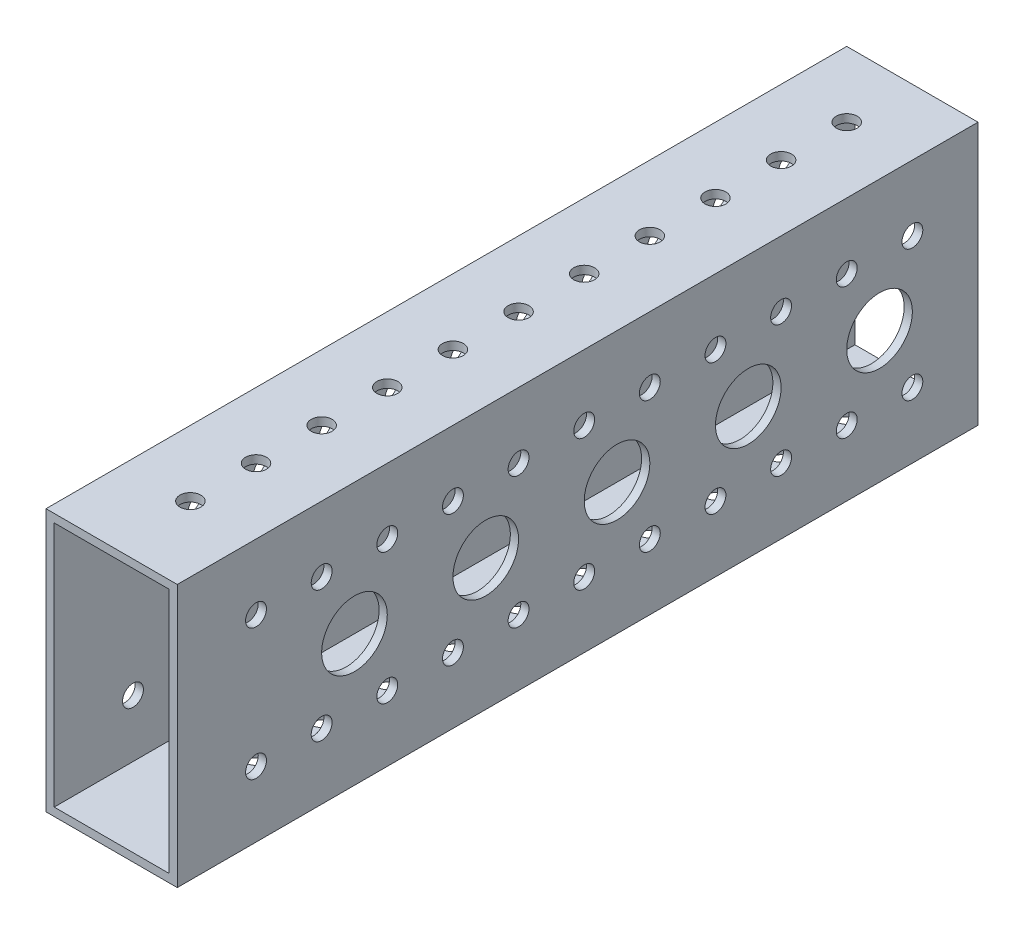
SolidWorks part; units mm, degrees
material "6061 Alloy"
ref_plane "Front Plane" through (0, 0, 0) normal (0, 0, 1) x (1, 0, 0)
ref_plane "Top Plane" through (0, 0, 0) normal (0, 1, 0) x (1, 0, 0)
ref_plane "Right Plane" through (0, 0, 0) normal (1, 0, 0) x (0, 0, -1)
sketch "Sketch1" plane through (0, 0, 0) normal (0, 0, 1) x (1, 0, 0)
  line L1 (0, 0) -> (25.4, 0)
  line L2 (0, 0) -> (0, 50.8)
  line L3 (0, 50.8) -> (25.4, 50.8)
  line L4 (25.4, 0) -> (25.4, 50.8)
  dimension "D1" = 25.4
  dimension "D2" = 50.8
extrude "Boss-Extrude1" add sketch "Sketch1" along normal blind 154.94
shell "Shell1" thickness 1.5875
hole_wizard "#21 (0.159) Diameter Hole1" positions "Sketch4" profile "Sketch3" hole size "#21" standard "ANSI Inch" end condition through all
sketch "Sketch4" plane through (25.4, 0, 0) normal (1, 0, 0) x (0, 0, -1)
  line L0 (0, 0) -> (0, 50.8) construction
  line L1 (-154.94, 50.8) -> (0, 50.8) construction
  point P0 (-12.7, 38.1)
  dimension "D1" = 12.7
  dimension "D2" = 12.7
sketch "Sketch3" plane through (25.4, 38.1, 12.7) normal (0, 1, 0) x (0, 0, -1)
  line L0 (0, 0) -> (0, 25.4)
  line L1 (0, 25.4) -> (2.0193, 25.4)
  line L2 (2.0193, 25.4) -> (2.0193, 0)
  line L5 (2.0193, 0) -> (0, 0)
  line L11 (0, -6.35) -> (0, 107.95) construction
  dimension "Thru Hole Dia." = 4.0386
  dimension "Thru Hole Depth" = 25.4
pattern_linear "LPattern1" count 11 spacing 12.7 along (0, 0, 1) count 2 spacing 25.4 along (0, -1, 0) of "#21 (0.159) Diameter Hole1"
hole_wizard "1/2 (0.5) Diameter Hole1" positions "Sketch5" profile "Sketch6" hole size "1/2" standard "ANSI Inch" end condition through all
sketch "Sketch5" plane through (25.4, 0, 0) normal (1, 0, 0) x (0, 0, -1)
  line L0 (0, 0) -> (0, 50.8) construction
  line L1 (-154.94, 0) -> (0, 0) construction
  point P0 (-19.05, 25.4)
  dimension "D1" = 19.05
  dimension "D2" = 25.4
sketch "Sketch6" plane through (25.4, 25.4, 19.05) normal (0, 1, 0) x (0, 0, -1)
  line L0 (0, 0) -> (0, 25.4)
  line L1 (0, 25.4) -> (6.35, 25.4)
  line L2 (6.35, 25.4) -> (6.35, 0)
  line L5 (6.35, 0) -> (0, 0)
  line L11 (0, -6.35) -> (0, 107.95) construction
  dimension "Thru Hole Dia." = 12.7
  dimension "Thru Hole Depth" = 25.4
pattern_linear "LPattern2" count 5 spacing 25.4 along (0, 0, 1) of "1/2 (0.5) Diameter Hole1"
hole_wizard "#21 (0.159) Diameter Hole2" positions "Sketch7" profile "Sketch8" hole size "#21" standard "ANSI Inch" end condition through all
sketch "Sketch7" plane through (0, 50.8, 0) normal (0, 1, 0) x (1, 0, 0)
  line L0 (25.4, 0) -> (0, 0) construction
  line L1 (0, -154.94) -> (0, 0) construction
  point P0 (12.7, -12.7)
  dimension "D1" = 12.7
  dimension "D2" = 12.7
sketch "Sketch8" plane through (12.7, 50.8, 12.7) normal (1, 0, 0) x (0, 0, 1)
  line L0 (0, 0) -> (0, 50.8)
  line L1 (0, 50.8) -> (2.0193, 50.8)
  line L2 (2.0193, 50.8) -> (2.0193, 0)
  line L5 (2.0193, 0) -> (0, 0)
  line L11 (0, -6.35) -> (0, 107.95) construction
  dimension "Thru Hole Dia." = 4.0386
  dimension "Thru Hole Depth" = 50.8
pattern_linear "LPattern3" count 11 spacing 12.7 along (0, 0, 1) of "#21 (0.159) Diameter Hole2"
